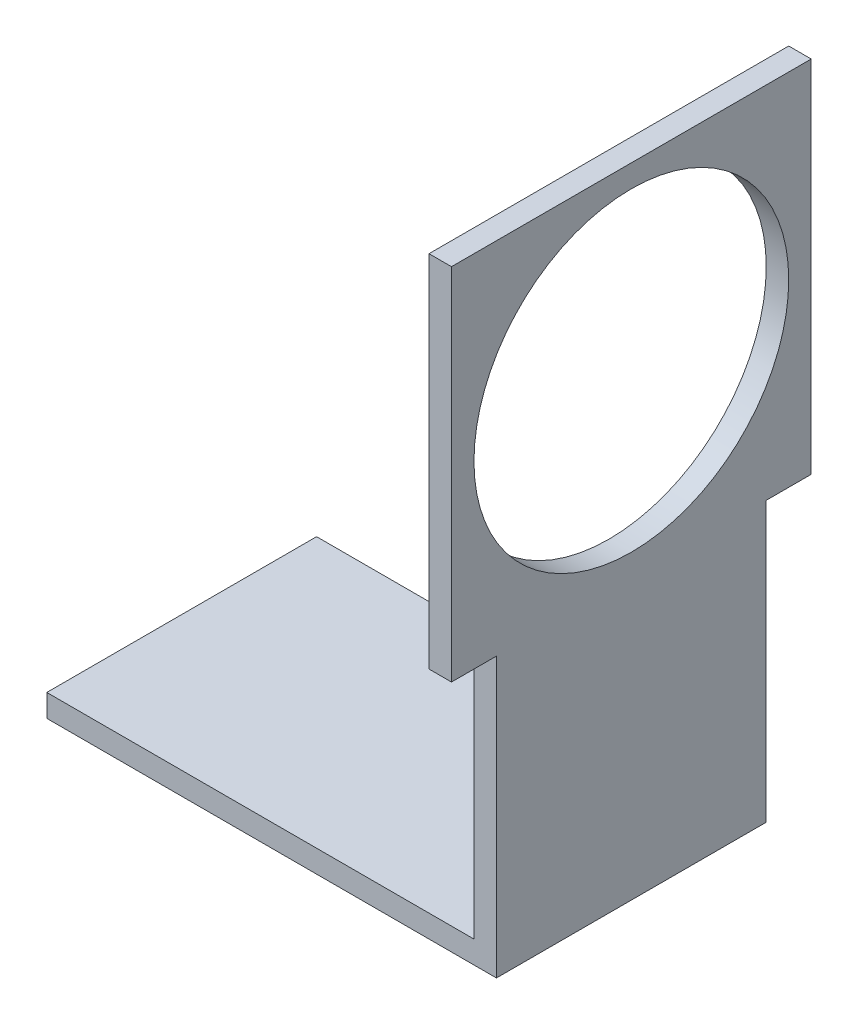
SolidWorks part; units mm, degrees
ref_plane "Front Plane" through (0, 0, 0) normal (0, 0, 1) x (1, 0, 0)
ref_plane "Top Plane" through (0, 0, 0) normal (0, 1, 0) x (1, 0, 0)
ref_plane "Right Plane" through (0, 0, 0) normal (1, 0, 0) x (0, 0, -1)
sketch "Sketch1" plane through (0, 0, 0) normal (0, 1, 0) x (1, 0, 0)
  line L1 (-93.0573, 30.7643) -> (6.9427, 30.7643)
  line L2 (-93.0573, 30.7643) -> (-93.0573, -29.2357)
  line L3 (-93.0573, -29.2357) -> (6.9427, -29.2357)
  line L4 (6.9427, 30.7643) -> (6.9427, -29.2357)
  dimension "D1" = 60
  dimension "D2" = 100
extrude "Boss-Extrude1" add sketch "Sketch1" along normal blind 5
sketch "Sketch2" plane through (0, 5, 0) normal (0, 1, 0) x (1, 0, 0)
  line L0 (-93.0573, -29.2357) -> (6.9427, -29.2357) construction
  line L1 (6.9427, 30.7643) -> (1.9427, 30.7643)
  line L2 (6.9427, 30.7643) -> (6.9427, -29.2357)
  line L3 (6.9427, -29.2357) -> (1.9427, -29.2357)
  line L4 (1.9427, 30.7643) -> (1.9427, -29.2357)
  dimension "D1" = 5
extrude "Boss-Extrude2" add sketch "Sketch2" along normal blind 57
sketch "Sketch4" plane through (6.9427, 0, 0) normal (1, 0, 0) x (0, 0, -1)
  line L0 (-29.2357, 62) -> (40.7643, 62)
  line L1 (40.7643, 62) -> (40.7643, 142)
  line L2 (40.7643, 142) -> (-39.2357, 142)
  line L3 (-39.2357, 142) -> (-39.2357, 62)
  line L4 (-39.2357, 62) -> (-29.2357, 62)
  line L5 (30.7643, 62) -> (30.7643, 0) construction
  dimension "D1" = 10
  dimension "D2" = 10
  dimension "D3" = 80
extrude "Boss-Extrude3" add sketch "Sketch4" against normal blind 5
sketch "Sketch5" plane through (6.9427, 0, 0) normal (1, 0, 0) x (0, 0, -1)
  line L0 (40.7643, 142) -> (-39.2357, 142) construction
  circle A0 centre (0.7643, 102) radius 35
  dimension "D1" = 70
  dimension "D2" = 40
extrude "Cut-Extrude1" cut sketch "Sketch5" against normal blind 5
